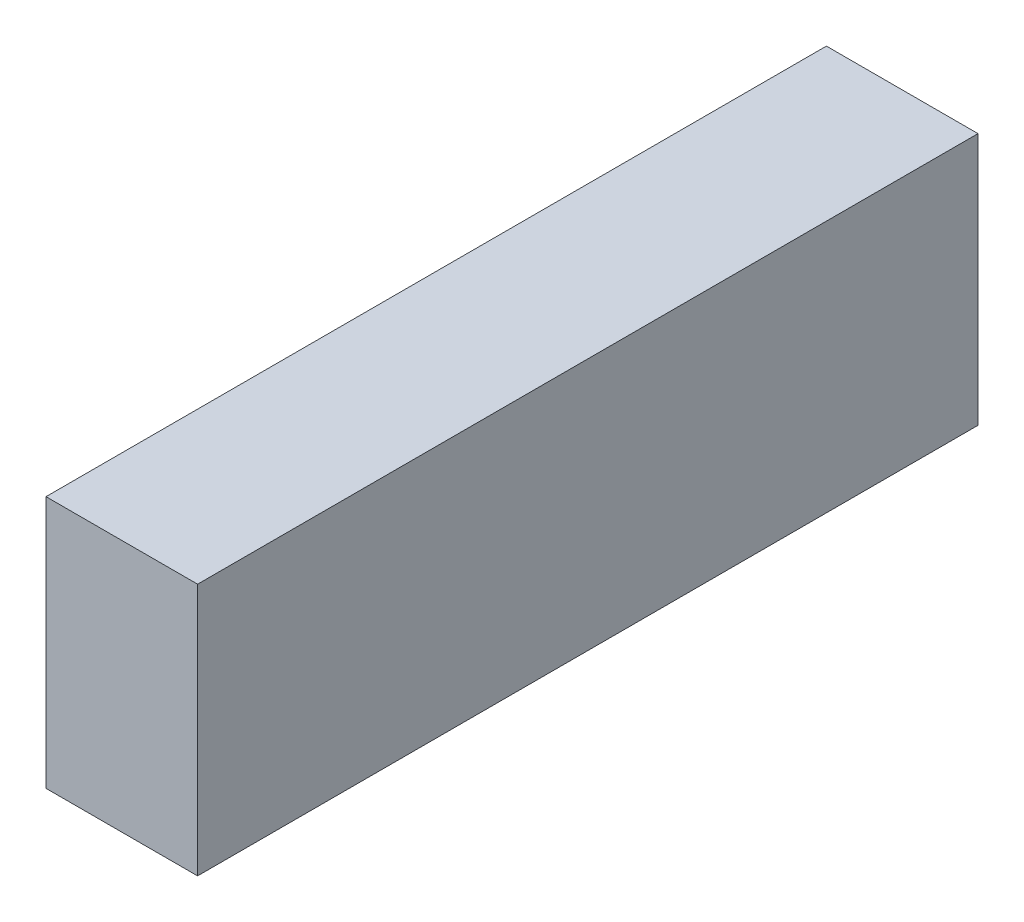
SolidWorks part; units mm, degrees
ref_plane "Front Plane" through (0, 0, 0) normal (0, 0, 1) x (1, 0, 0)
ref_plane "Top Plane" through (0, 0, 0) normal (0, 1, 0) x (1, 0, 0)
ref_plane "Right Plane" through (0, 0, 0) normal (1, 0, 0) x (0, 0, -1)
sketch "Sketch1" plane through (0, 0, 0) normal (0, 0, 1) x (1, 0, 0)
  line L1 (13.5, 22.5) -> (-13.5, 22.5)
  line L2 (13.5, 22.5) -> (13.5, -22.5)
  line L3 (13.5, -22.5) -> (-13.5, -22.5)
  line L4 (-13.5, 22.5) -> (-13.5, -22.5)
  line L5 (13.5, 22.5) -> (-13.5, -22.5) construction
  line L6 (13.5, -22.5) -> (-13.5, 22.5) construction
  point P0 (0, 0)
  dimension "D1" = 45
  dimension "D2" = 27
extrude "Boss-Extrude1" add sketch "Sketch1" along normal mid plane 139
